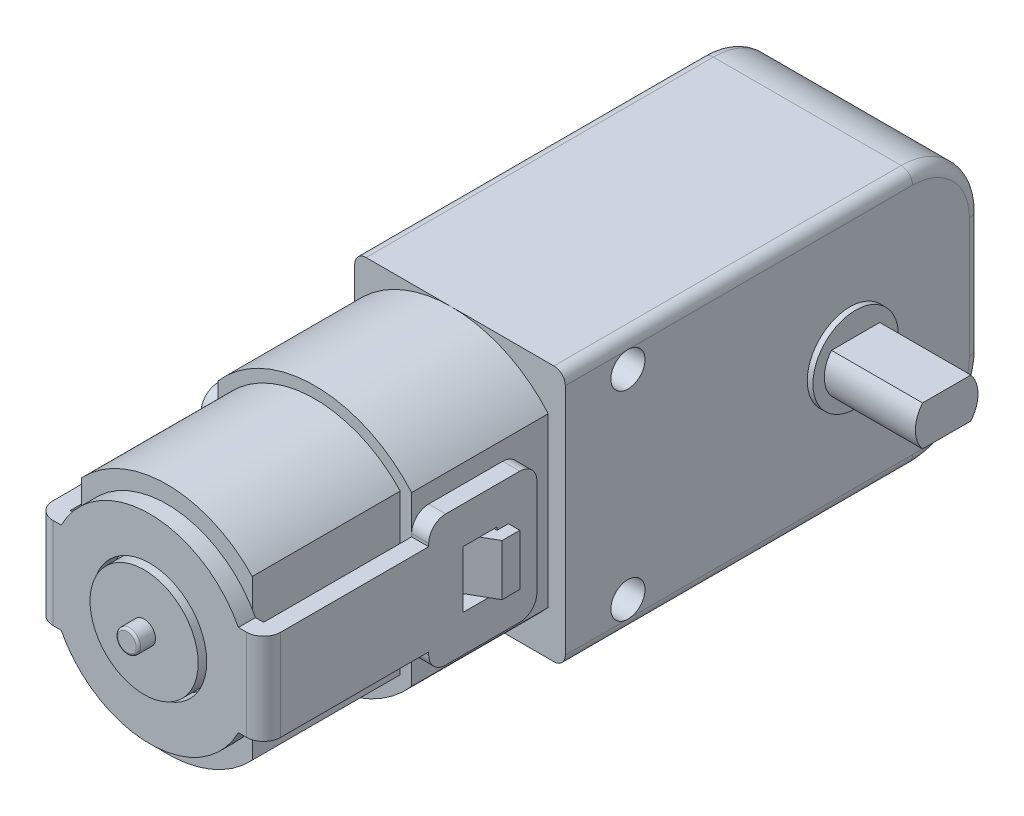
SolidWorks part; units mm, degrees
ref_plane "Plano frontal" through (0, 0, 0) normal (0, 0, 1) x (1, 0, 0)
ref_plane "Plano superior" through (0, 0, 0) normal (0, 1, 0) x (1, 0, 0)
ref_plane "Plano direito" through (0, 0, 0) normal (1, 0, 0) x (0, 0, -1)
sketch "Esboço1" plane through (0, 0, 0) normal (1, 0, 0) x (0, 0, -1)
  line L0 (0, 0) -> (0, 50000) construction
  line L1 (11.5, 11.25) -> (-25, 11.25)
  line L2 (11.5, 11.25) -> (11.5, -11.25)
  line L3 (11.5, -11.25) -> (-25, -11.25)
  line L4 (-25, 11.25) -> (-25, -11.25)
  line L5 (0, 0) -> (50000, 0) construction
  dimension "D1" = 22.5
  dimension "D2" = 11.5
  dimension "D3" = 36.5
extrude "Ressalto-extrusão1" add sketch "Esboço1" along normal mid plane 18.5
fillet "Filete1" radius 6 2 edges at (0, -11.25, -11.5) (0, 11.25, -11.5)
sketch "Esboço2" plane through (0, 0, 25) normal (0, 0, 1) x (1, 0, 0)
  line L0 (0, 0) -> (0, 50000) construction
  line L1 (0, 0) -> (50000, 0) construction
  line L2 (9.25, -11.25) -> (-9.25, -11.25) construction
  line L3 (9.25, 11.25) -> (-9.25, 11.25) construction
  line L4 (7.75, 7.3697) -> (7.75, -7.3697)
  line L5 (-9.25, -7.3697) -> (-9.25, 7.3697)
  line L6 (-9.25, 11.25) -> (-9.25, -11.25) construction
  line L7 (9.25, 11.25) -> (9.25, -11.25) construction
  arc A0 (-9.25, -7.3697) -> (7.75, -7.3697) centre (-0.75, 0) ccw
  arc A1 (7.75, 7.3697) -> (-9.25, 7.3697) centre (-0.75, 0) ccw
  dimension "D1" = 1.5
extrude "Ressalto-extrusão2" add sketch "Esboço2" along normal blind 12
sketch "Esboço3" plane through (0, 0, 37) normal (0, 0, 1) x (1, 0, 0)
  line L0 (-8.25, 6.9866) -> (-8.25, -6.9866)
  line L1 (6.75, -6.9866) -> (6.75, 6.9866)
  line L2 (-9.25, 7.3697) -> (-9.25, -7.3697)
  line L3 (7.75, -7.3697) -> (7.75, 7.3697)
  line L4 (-9.25, 7.3697) -> (-9.25, -7.3697) construction
  line L5 (7.75, -7.3697) -> (7.75, 7.3697) construction
  arc A0 (-8.25, -6.9866) -> (6.75, -6.9866) centre (-0.75, 0) ccw
  arc A1 (6.75, 6.9866) -> (-8.25, 6.9866) centre (-0.75, 0) ccw
  arc A2 (7.75, 7.3697) -> (-9.25, 7.3697) centre (-0.75, 0) ccw
  arc A3 (-9.25, -7.3697) -> (7.75, -7.3697) centre (-0.75, 0) ccw
  arc A4 (7.75, 7.3697) -> (-9.25, 7.3697) centre (-0.75, 0) ccw construction
  arc A5 (-9.25, -7.3697) -> (7.75, -7.3697) centre (-0.75, 0) ccw construction
  dimension "D1" = 0
  dimension "D2" = 1
extrude "Ressalto-extrusão3" add sketch "Esboço3" along normal blind 13
sketch "Esboço4" plane through (9.25, 0, 0) normal (1, 0, 0) x (0, 0, -1)
  circle A0 centre (0, 0) radius 3.75
  dimension "D1" = 7.5
extrude "Ressalto-extrusão4" add sketch "Esboço4" along normal blind 0.5
sketch "Esboço5" plane through (7.75, 0, 0) normal (1, 0, 0) x (0, 0, -1)
  line L0 (-37, -7.3697) -> (-37, 7.3697) construction
  line L1 (-27.5, 5.75) -> (-37, 5.75)
  line L2 (-27.5, 5.75) -> (-27.5, -5.75)
  line L3 (-27.5, -5.75) -> (-37, -5.75)
  line L4 (-37, 5.75) -> (-37, -5.75)
  line L5 (0, 0) -> (-50000, 0) construction
  line L6 (0, 0) -> (0, 50000) construction
  line L7 (-25, 11.25) -> (-25, -11.25) construction
  dimension "D1" = 2.5
  dimension "D2" = 11.5
extrude "Ressalto-extrusão5" add sketch "Esboço5" along normal blind 1.5 separate body
sketch "Esboço6" plane through (0, 0, 37) normal (0, 0, 1) x (1, 0, 0)
  line L0 (9.25, 5.75) -> (9.25, -5.75) construction
  line L1 (9.25, 4) -> (7.75, 4)
  line L2 (9.25, 4) -> (9.25, -4)
  line L3 (9.25, -4) -> (7.75, -4)
  line L4 (7.75, 4) -> (7.75, -4)
  line L5 (7.75, -7.3697) -> (7.75, 7.3697) construction
  line L6 (0, 0) -> (-50000, 0) construction
  dimension "D1" = 8
extrude "Ressalto-extrusão6" add sketch "Esboço6" along normal up to surface (13 mm away) up to face at (-0.75, 0, 50)
sketch "Esboço7" plane through (0, 0, 50) normal (0, 0, 1) x (1, 0, 0)
  line L0 (9.25, 4) -> (7.0322, 4)
  line L1 (9.25, 4) -> (9.25, -4)
  line L2 (9.25, -4) -> (7.0322, -4)
  line L3 (-0.75, 8.75) -> (-0.75, 0) construction
  line L4 (-10.75, -4) -> (-8.5322, -4)
  line L5 (-10.75, 4) -> (-10.75, -4)
  line L6 (-10.75, 4) -> (-8.5322, 4)
  arc A0 (7.0322, 4) -> (-8.5322, 4) centre (-0.75, 0) ccw
  arc A1 (6.75, 6.9866) -> (-8.25, 6.9866) centre (-0.75, 0) ccw construction
  arc A2 (-8.5322, -4) -> (7.0322, -4) centre (-0.75, 0) ccw
  circle A3 centre (-0.75, 0) radius 5
  dimension "D1" = 17.5
  dimension "D2" = 10
sketch "Esboço8" plane through (0, 0, 50) normal (0, 0, 1) x (1, 0, 0)
  circle A0 centre (-0.75, 0) radius 4.75
  dimension "D1" = 9.5
extrude "Ressalto-extrusão7" add sketch "Esboço8" along normal blind 2
extrude "Ressalto-extrusão8" add sketch "Esboço7" along normal blind 1.5
ref_plane "Plano1" through (-0.75, 8.75, 51.5) normal (-1, 0, 0) x (0, 0, 1)
sketch "Esboço10" plane through (0, 0, 50) normal (0, 0, -1) x (-1, 0, 0)
  line L0 (10.75, -4) -> (8.5322, -4) construction
  line L1 (10.75, 4) -> (9.25, 4)
  line L2 (10.75, 4) -> (10.75, -4)
  line L3 (10.75, -4) -> (9.25, -4)
  line L4 (9.25, 4) -> (9.25, -4)
  line L5 (-9.25, 4) -> (-7.75, 4) construction
extrude "Ressalto-extrusão9" add sketch "Esboço10" along normal up to surface (13 mm away) up to face at (8.6875, 5.3125, 37)
sketch "Esboço11" plane through (0, 0, 37) normal (0, 0, -1) x (-1, 0, 0)
  line L0 (10.75, -4) -> (10.75, 4) construction
  line L1 (10.75, 5.75) -> (9.25, 5.75)
  line L2 (10.75, 5.75) -> (10.75, -5.75)
  line L3 (10.75, -5.75) -> (9.25, -5.75)
  line L4 (9.25, 5.75) -> (9.25, -5.75)
  line L5 (9.25, 4) -> (9.25, -4) construction
  line L6 (-9.25, -5.75) -> (-9.25, 5.75) construction
  line L7 (-9.25, 5.75) -> (-7.75, 5.75) construction
extrude "Ressalto-extrusão10" add sketch "Esboço11" along normal up to surface (9.5 mm away) up to face at (8.5, 0, 27.5)
fillet "Filete2" radius 1.5 10 edges at (8.5, -5.75, 37) (8.5, -5.75, 27.5) (8.5, 5.75, 27.5) (8.5, 5.75, 37) (9.25, 0, 51.5) (-10.75, 0, 51.5) (-10, -5.75, 27.5) (-10, -5.75, 37) (-10, 5.75, 37) (-10, 5.75, 27.5)
sketch "Esboço12" plane through (9.25, 0, 0) normal (1, 0, 0) x (0, 0, -1)
  line L0 (-25, 11.25) -> (-25, -11.25) construction
  line L1 (-31, 2.5) -> (-34, 2.5)
  line L2 (-31, 2.5) -> (-31, -2.5)
  line L3 (-31, -2.5) -> (-34, -2.5)
  line L4 (-34, 2.5) -> (-34, -2.5)
  line L5 (0, 0) -> (-50000, 0) construction
  dimension "D1" = 6
  dimension "D2" = 3
  dimension "D3" = 5
extrude "Corte-extrusão1" cut sketch "Esboço12" against normal through all
sketch "Esboço14" plane through (0, 0, 0) normal (0, 1, 0) x (1, 0, 0)
  line L0 (7.75, -33) -> (10.25, -31.5566)
  line L1 (7.75, -37) -> (7.75, -25) construction
  line L2 (10.25, -31.5566) -> (10.25, -30)
  line L3 (10.25, -30) -> (9.25, -30)
  line L4 (9.25, -35.5) -> (9.25, -29) construction
  line L5 (9.25, -30) -> (9.25, -31)
  line L6 (7.75, -31) -> (9.25, -31) construction
  line L7 (9.25, -31) -> (7.75, -31)
  line L8 (7.75, -31) -> (7.75, -33)
  dimension "D1" = 2.5
  dimension "D2" = 1
  dimension "D3" = 60
  dimension "D4" = 2
extrude "Ressalto-extrusão11" add sketch "Esboço14" along normal mid plane 4.5
mirror "Espelhar6" about plane through (-0.75, 8.75, 51.5) normal (-1, 0, 0) of "Ressalto-extrusão11"
sketch "Esboço15" plane through (0, 0, 52) normal (0, 0, 1) x (1, 0, 0)
  circle A0 centre (-0.75, 0) radius 1
  dimension "D1" = 2
extrude "Ressalto-extrusão12" add sketch "Esboço15" along normal blind 1.5
sketch "Esboço16" plane through (9.75, 0, 0) normal (1, 0, 0) x (0, 0, -1)
  line L0 (0, 0) -> (-50000, 0) construction
  line L1 (-2.1213, 1.75) -> (2.1213, 1.75)
  line L3 (2.1213, -1.75) -> (-2.1213, -1.75)
  arc A0 (2.1213, -1.75) -> (2.1213, 1.75) centre (0, 0) ccw
  arc A1 (-2.1213, 1.75) -> (-2.1213, -1.75) centre (0, 0) ccw
  dimension "D1" = 5.5
  dimension "D2" = 3.5
extrude "Ressalto-extrusão13" add sketch "Esboço16" along normal blind 8
fillet "Filete4" radius 1 10 edges at (-9.25, -11.25, 9.75) (9.25, -11.25, 9.75) (9.25, -9.4926, -9.7426) (-9.25, -9.4926, -9.7426) (9.25, 0, -11.5) (-9.25, 0, -11.5) (9.25, 9.4926, -9.7426) (-9.25, 9.4926, -9.7426) (9.25, 11.25, 9.75) (-9.25, 11.25, 9.75)
sketch "Esboço17" plane through (9.25, 0, 0) normal (1, 0, 0) x (0, 0, -1)
  line L0 (-19.5, 8.75) -> (-19.5, -8.75) construction
  line L1 (-19.5, 0) -> (0, 0) construction
  line L2 (-25, 11.25) -> (-25, 7.3697) construction
  circle A0 centre (-19.5, 8.75) radius 1.5
  circle A1 centre (-19.5, -8.75) radius 1.5
  dimension "D2" = 3
  dimension "D3" = 4
  dimension "D1" = 17.5
extrude "Corte-extrusão2" cut sketch "Esboço17" against normal through all
sketch "Esboço19" plane through (0, 0, 0) normal (1, 0, 0) x (0, 0, -1)
  line L0 (11.5, 3) -> (14.4508, 2.459)
  line L1 (11.5, 5.25) -> (11.5, -5.25) construction
  line L2 (14.4508, -2.459) -> (11.5, -3)
  line L3 (11.5, -3) -> (11.5, 3)
  line L4 (0, 0) -> (50000, 0) construction
  arc A0 (14.4508, 2.459) -> (14.4508, -2.459) centre (14, 0) cw
  circle A1 centre (14, 0) radius 1.5
  dimension "D2" = 5
  dimension "D3" = 3
  dimension "D4" = 2.5
  dimension "D1" = 6
extrude "Ressalto-extrusão14" add sketch "Esboço19" along normal mid plane 3
fillet "Filete5" radius 1 2 edges at (0, 3, -11.5) (0, -3, -11.5)
fillet "Filete6" radius 0.2 1 edges at (0.25, 0, 53.5)
